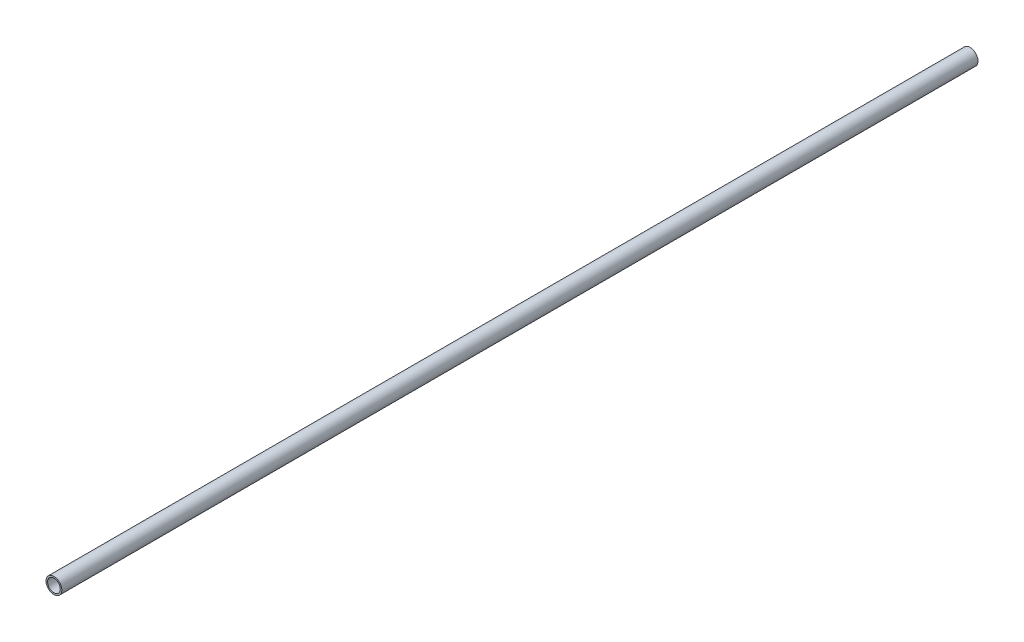
SolidWorks part; units mm, degrees
material "McMaster Carbon Fiber Twill Tube"
ref_plane "Front Plane" through (0, 0, 0) normal (0, 0, 1) x (1, 0, 0)
ref_plane "Top Plane" through (0, 0, 0) normal (0, 1, 0) x (1, 0, 0)
ref_plane "Right Plane" through (0, 0, 0) normal (1, 0, 0) x (0, 0, -1)
sketch "Sketch1" plane through (0, 0, 0) normal (0, 0, 1) x (1, 0, 0)
  circle A0 centre (0, 0) radius 15.7988 construction
  circle A1 centre (0, 0) radius 12.7 construction
  point P4 (12.7, 0)
  point P5 (15.7988, 0)
  dimension "OD" = 31.5976
  dimension "ID" = 25.4
  dimension "Wall Thickness" = 3.0988
sketch "Sketch2" plane through (0, 0, 0) normal (1, 0, 0) x (0, 0, -1)
  line L0 (-914.4, 0) -> (914.4, 0) construction
  line L1 (-914.4, -15.7988) -> (-914.4, 15.7988) construction
  line L2 (-914.4, 15.7988) -> (914.4, 15.7988) construction
  line L3 (914.4, -15.7988) -> (914.4, 15.7988) construction
  line L5 (-914.4, -15.7988) -> (914.4, -15.7988) construction
  point P0 (-882.8024, 0)
  point P3 (0, 0)
  point P7 (0, 15.7988)
  point P8 (882.8024, 0)
  point P11 (-914.4, 0)
  point P13 (914.4, 0)
  dimension "Length" = 1828.8
  dimension "D1" = 31.5976
  dimension "D2" = 31.5976
sketch "Sketch3" plane through (0, 0, 0) normal (0, 0, 1) x (1, 0, 0)
  circle A0 centre (0, 0) radius 12.7 construction
  circle A1 centre (0, 0) radius 15.7988 construction
  circle A2 centre (0, 0) radius 12.7
  circle A3 centre (0, 0) radius 15.7988
extrude "Boss-Extrude1" add sketch "Sketch3" along normal up to vertex (914.4 mm away) and the other way up to vertex (914.4 mm away) up to point (0, 0, 914.4) other way up to point (0, 0, -914.4)
equation "\"D1@Sketch2\"=\"OD@Sketch1\""
equation "\"D2@Sketch2\"=\"D1@Sketch2\""
